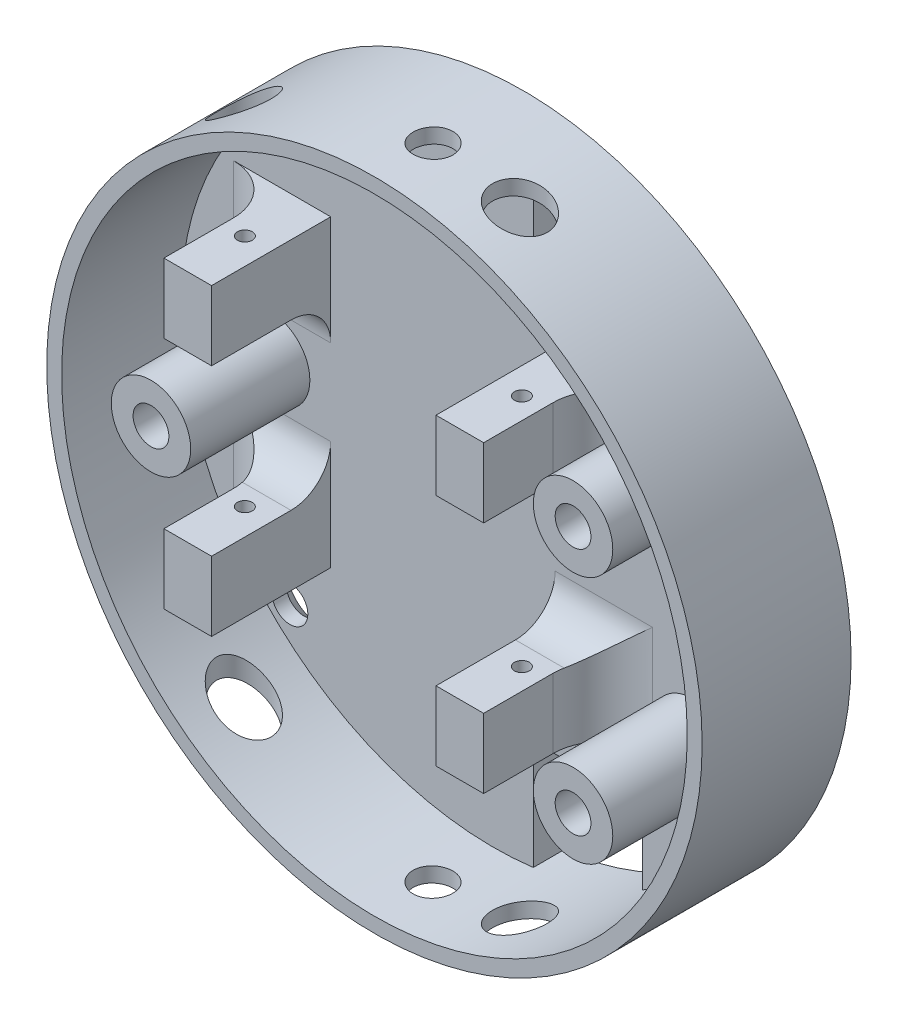
SolidWorks part; units mm, degrees
material "PEI"
ref_plane "Alzado" through (0, 0, 0) normal (0, 0, 1) x (1, 0, 0)
ref_plane "Planta" through (0, 0, 0) normal (0, 1, 0) x (1, 0, 0)
ref_plane "Vista lateral" through (0, 0, 0) normal (1, 0, 0) x (0, 0, -1)
sketch "Croquis1" plane through (0, 0, 0) normal (0, 0, 1) x (1, 0, 0)
  circle A0 centre (0, 0) radius 33
  dimension "D1" = 66
extrude "Saliente-Extruir1" add sketch "Croquis1" along normal blind 3
sketch "Croquis2" plane through (0, 0, 3) normal (0, 0, 1) x (1, 0, 0)
  line L0 (-21.2, -15.3) -> (-16.4, -15.3)
  line L1 (11, -15.3) -> (6.2, -15.3)
  line L2 (-21.2, -15.3) -> (-21.2, -8.3)
  line L3 (-21.2, -8.3) -> (-16.4, -8.3)
  line L4 (-16.4, -8.3) -> (-16.4, -15.3)
  line L5 (6.2, -15.3) -> (6.2, -8.3)
  line L6 (6.2, -8.3) -> (11, -8.3)
  line L7 (11, -8.3) -> (11, -15.3)
  line L8 (6.2, -15.3) -> (11, -15.3)
  line L9 (0, 0) -> (12.8027, 0) construction
  line L10 (11, 8.3) -> (11, 15.3)
  line L11 (11, 15.3) -> (6.2, 15.3)
  line L12 (6.2, 8.3) -> (11, 8.3)
  line L13 (6.2, 15.3) -> (6.2, 8.3)
  line L14 (-16.4, 8.3) -> (-16.4, 15.3)
  line L15 (-21.2, 15.3) -> (-16.4, 15.3)
  line L16 (-21.2, 15.3) -> (-21.2, 8.3)
  line L17 (-21.2, 8.3) -> (-16.4, 8.3)
  point P2 (0, -15.3)
  point P3 (-16.4, -15.3)
  point P13 (8.6, -15.3)
  point P16 (8.6, 15.3)
  dimension "D1" = 32.2
  dimension "D2" = 11
  dimension "D4" = 4.8
  dimension "D5" = 4.8
  dimension "D6" = 15.3
  dimension "D7" = 7
  dimension "D3" = 7
extrude "Saliente-Extruir2" add sketch "Croquis2" along normal blind 12 contours L7 L6 L5 L1 | L4 L3 L2 L0 | L16 L17 L14 L15 | L11 L13 L12 L10
sketch "Croquis3" plane through (0, -15.3, 0) normal (0, -1, 0) x (1, 0, 0)
  line L0 (-21.2, 15) -> (-21.2, 3) construction
  line L3 (11, 15) -> (11, 3) construction
  line L6 (-21.2, 3) -> (-16.4, 3) construction
  circle A0 centre (-19.05, 9) radius 0.75
  circle A1 centre (8.85, 9) radius 0.75
  dimension "D1" = 1.5
  dimension "D2" = 2.15
  dimension "D3" = 2.15
  dimension "D4" = 6
extrude "Cortar-Extruir1" cut sketch "Croquis3" against normal up to surface (30.6 mm away) up to face at (8.6, 15.3, 9)
ref_plane "Plano1" through (0, -33, 0) normal (0, -1, 0) x (-1, 0, 0)
ref_plane "Plano2" through (0, -29.45, 0) normal (0, -1, 0) x (-1, 0, 0)
sketch "Croquis6" plane through (0, 0, 0) normal (0, 0, -1) x (-1, 0, 0)
  line L0 (-20.5061, 20.5061) -> (0, 0) construction
  line L1 (0, 0) -> (0, -33) construction
  circle A0 centre (-20, 12.5) radius 1.8
  circle A1 centre (-20, -12.5) radius 1.8
  circle A2 centre (22.5, 0) radius 1.8
  circle A3 centre (0, 0) radius 29 construction
  circle A4 centre (0, 0) radius 33 construction
  circle A5 centre (-20.5061, 20.5061) radius 1.8
  circle A6 centre (20.5061, 20.5061) radius 1.8
  circle A7 centre (20.5061, -20.5061) radius 1.8
  circle A8 centre (-20.5061, -20.5061) radius 1.8
  point P24 (0, 0)
  dimension "D1" = 3.6
  dimension "D2" = 3.6
  dimension "D3" = 3.6
  dimension "D10" = 3.6
  dimension "D6" = 25
  dimension "D7" = 12.5
  dimension "D4" = 22.5
  dimension "D5" = 20
  dimension "D8" = 4
  dimension "D9" = 135
  dimension "D11" = 4
extrude "Cortar-Extruir4" cut sketch "Croquis6" against normal up to surface (3 mm away) up to face at (-18.8, -11.8, 3)
sketch "Croquis7" plane through (0, 0, 3) normal (0, 0, 1) x (1, 0, 0)
  circle A2 centre (0, 0) radius 33 construction
  circle A9 centre (0, 0) radius 33
  circle A11 centre (0, 0) radius 31.5
  dimension "D1" = 1.5
extrude "Saliente-Extruir3" add sketch "Croquis7" along normal blind 12
ref_plane "Plano3" through (0, -33, 0) normal (0, -1, 0) x (-1, 0, 0)
sketch "Croquis8" plane through (0, -33, 0) normal (0, -1, 0) x (-1, 0, 0)
  line L0 (-33, -15) -> (33, -15) construction
  circle A1 centre (-8.75, -9.1) radius 2.75
  circle A3 centre (19.05, -9.1) radius 2.75
  circle A4 centre (0, -9.1) radius 2
  dimension "D1" = 4
  dimension "D5" = 5.5
  dimension "D6" = 5.5
  dimension "D2" = 5.9
  dimension "D3" = 8.75
  dimension "D4" = 19.05
extrude "Cortar-Extruir5" cut sketch "Croquis8" against normal blind 14
sketch "Croquis9" plane through (0, 0, 3) normal (0, 0, 1) x (1, 0, 0)
  circle A0 centre (20, -12.5) radius 1.8 construction
  circle A1 centre (20, -12.5) radius 1.8
  circle A2 centre (-22.5, 0) radius 1.8 construction
  circle A3 centre (-22.5, 0) radius 1.8
  circle A4 centre (20, 12.5) radius 1.8 construction
  circle A5 centre (20, 12.5) radius 1.8
  circle A6 centre (-22.5, 0) radius 4
  circle A7 centre (20, -12.5) radius 4
  circle A8 centre (20, 12.5) radius 4
  dimension "D1" = 8
extrude "Saliente-Extruir4" add sketch "Croquis9" along normal up to surface (12 mm away) up to face at (33, 0, 15)
sketch "Sketch3" plane through (0, 0, 0) normal (0, 0, -1) x (-1, 0, 0)
  line L1 (4.1, -7.6) -> (-4.1, -7.6)
  line L2 (4.1, -7.6) -> (4.1, 7.6)
  line L3 (4.1, 7.6) -> (-4.1, 7.6)
  line L4 (-4.1, -7.6) -> (-4.1, 7.6)
  line L5 (4.1, -7.6) -> (-4.1, 7.6) construction
  line L6 (4.1, 7.6) -> (-4.1, -7.6) construction
  point P0 (0, 0)
  dimension "D1" = 8.2
  dimension "D2" = 15.2
extrude "Cut-Extrude1" cut sketch "Sketch3" against normal blind 0.5
hole_wizard "Avellanado para tornillo con cabeza plana de M31" positions "Sketch4" profile "Sketch5" countersink size "M3" standard "Ansi Metric" end condition through all
sketch "Sketch4" plane through (0, 0, 0) normal (0, 0, -1) x (-1, 0, 0)
  point P0 (-20, 12.5)
  point P3 (-20, -12.5)
  point P6 (22.5, 0)
sketch "Sketch5" plane through (20, 12.5, 0) normal (1, 0, 0) x (0, 1, 0)
  line L0 (0, 0) -> (0, 15)
  line L1 (0, 15) -> (1.8, 15)
  line L2 (1.8, 15) -> (1.8, 1.35)
  line L3 (1.8, 1.35) -> (3.15, 0)
  line L5 (3.15, 0) -> (0, 0)
  line L6 (-1.8, 1.35) -> (-3.15, 0) construction
  line L11 (0, -6.35) -> (0, 107.95) construction
  dimension "Thru Hole Dia." = 3.6
  dimension "Thru Hole Depth" = 15
  dimension "Near C'Sink Dia." = 6.3
  dimension "Near C'Sink Angle" = 90
mirror "Mirror1" about plane through (0, 0, 0) normal (0, 1, 0) of "Cortar-Extruir5"
fillet "Fillet5" radius 4 4 edges at (-18.8, 8.3, 3) (8.6, 8.3, 3) (8.6, -8.3, 3) (-18.8, -8.3, 3)
fillet "Fillet6" radius 5 4 edges at (-21.2, 9.8, 3) (-21.2, -9.8, 3) (11, 9.8, 3) (11, -9.8, 3)
sketch "Sketch9" plane through (0, 0, 0) normal (0, 0, -1) x (-1, 0, 0)
  line L0 (-4, -31.245) -> (-4, -20.245)
  line L1 (-4, -20.245) -> (-7, -20.245)
  line L2 (-15, -22.7993) -> (-15, -27.6993)
  line L4 (-7, -20.245) -> (-7, -22.7993)
  line L5 (-7, -22.7993) -> (-15, -22.7993)
  arc A0 (-4, -31.245) -> (-15, -27.6993) centre (0, 0) cw
  dimension "D2" = 11
  dimension "D1" = 31.5
  dimension "D6" = 4.9
  dimension "D9" = 8.4457
  dimension "D3" = 15
  dimension "D4" = 8
  dimension "D5" = 3
extrude "Cut-Extrude4" cut sketch "Sketch9" against normal up to surface (3 mm away) up to face at (31.5, 0, 3)
sketch "Sketch10" plane through (0, 0, 0) normal (0, 0, -1) x (-1, 0, 0)
  line L0 (-7, -22.7993) -> (-15, -22.7993) construction
  line L1 (-4, -22.7993) -> (3.1, -22.7993)
  line L2 (-4, -22.7993) -> (-4, -30.8993)
  line L3 (-4, -30.8993) -> (3.1, -30.8993)
  line L4 (3.1, -22.7993) -> (3.1, -30.8993)
  line L5 (-4, -22.7993) -> (3.1, -30.8993) construction
  line L6 (-4, -30.8993) -> (3.1, -22.7993) construction
  line L7 (-4, -31.245) -> (-4, -20.245) construction
  line L8 (0, 0) -> (-11.9554, 0) construction
  line L9 (-4, 30.8993) -> (3.1, 22.7993) construction
  line L10 (-4, 22.7993) -> (3.1, 30.8993) construction
  line L11 (3.1, 22.7993) -> (3.1, 30.8993)
  line L12 (-4, 30.8993) -> (3.1, 30.8993)
  line L13 (-4, 22.7993) -> (-4, 30.8993)
  line L14 (-4, 22.7993) -> (3.1, 22.7993)
  point P0 (-0.45, -26.8493)
  point P16 (-0.45, 26.8493)
  dimension "D1" = 7.1
  dimension "D2" = 8.1
extrude "Cut-Extrude5" cut sketch "Sketch10" against normal blind 0.4
mirror "Mirror3" about plane through (0, 0, 0) normal (0, 1, 0) of "Cut-Extrude4"
hole_wizard "Refrentado para tornillo tapón con cabeza plana de clavija de M31" positions "Croquis10" profile "Croquis11" countersink size "M3" standard "Ansi Metric" end condition up to next
sketch "Croquis10" plane through (0, 0, 0) normal (0, 0, -1) x (-1, 0, 0)
  point P0 (-20.5061, -20.5061)
  point P3 (20.5061, -20.5061)
  point P6 (20.5061, 20.5061)
  point P9 (-20.5061, 20.5061)
sketch "Croquis11" plane through (20.5061, -20.5061, 0) normal (1, 0, 0) x (0, 1, 0)
  line L0 (0, 0) -> (0, 15)
  line L1 (0, 15) -> (1.8, 15)
  line L2 (1.8, 15) -> (1.8, 1.56)
  line L3 (1.8, 1.56) -> (3.36, 0)
  line L5 (3.36, 0) -> (0, 0)
  line L6 (-1.8, 1.56) -> (-3.36, 0) construction
  line L11 (0, -6.35) -> (0, 107.95) construction
  dimension "Diámetro de taladro hasta el siguiente" = 3.6
  dimension "Profundidad de taladro hasta el siguiente" = 15
  dimension "Diámetro de avellanado cercano" = 6.72
  dimension "Ángulo de avellanado cercano" = 90
equation "\"D2@Croquis6\"=\"D1@Croquis6\""
equation "\"D3@Croquis6\"=\"D1@Croquis6\""
equation "\"D7@Croquis6\"=\"D6@Croquis6\"/2"
equation "\"D6@Croquis8\"=\"D5@Croquis8\""
equation "\"D3@Croquis2\"=\"D7@Croquis2\""
equation "\"D1@Sketch9\"=63/2"
